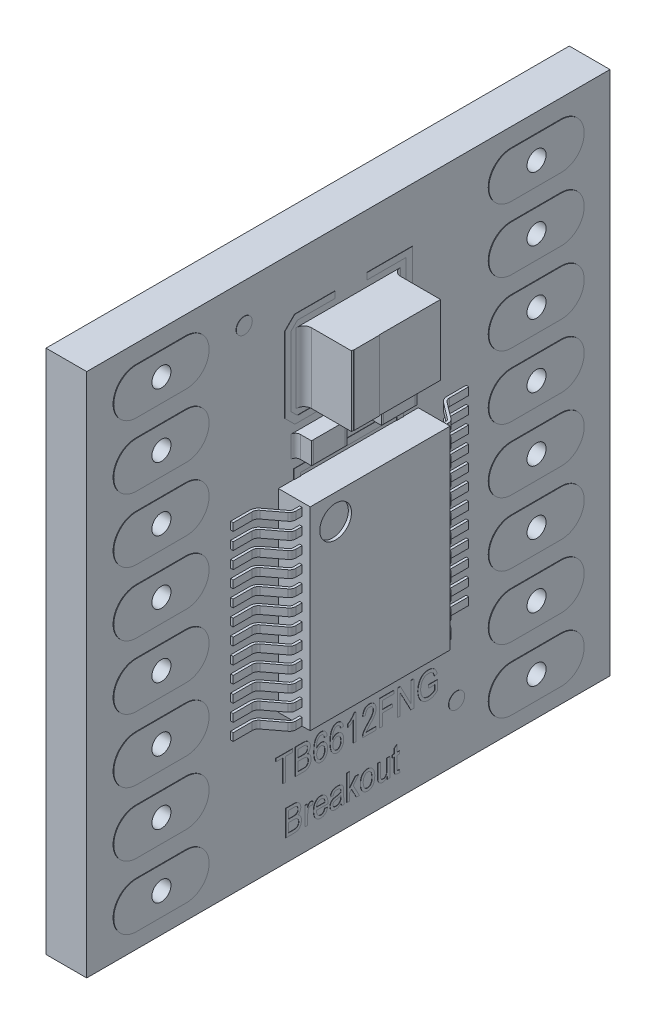
SolidWorks part; units mm, degrees
ref_plane "Front Plane" through (0, 0, 0) normal (0, 0, 1) x (1, 0, 0)
ref_plane "Top Plane" through (0, 0, 0) normal (0, 1, 0) x (1, 0, 0)
ref_plane "Right Plane" through (0, 0, 0) normal (1, 0, 0) x (0, 0, -1)
sketch "Sketch1" plane through (0, 0, 0) normal (1, 0, 0) x (0, 0, -1)
  line L1 (-10.4521, 10.4902) -> (10.4521, 10.4902)
  line L2 (-10.4521, 10.4902) -> (-10.4521, -10.4902)
  line L3 (-10.4521, -10.4902) -> (10.4521, -10.4902)
  line L4 (10.4521, 10.4902) -> (10.4521, -10.4902)
  line L5 (-10.4521, 10.4902) -> (10.4521, -10.4902) construction
  line L6 (-10.4521, -10.4902) -> (10.4521, 10.4902) construction
  point P0 (0, 0)
  dimension "D1" = 20.9804
  dimension "D2" = 20.9042
extrude "Boss-Extrude1" add sketch "Sketch1" along normal blind 1.6256
sketch "Sketch2" plane through (1.6256, 0, 0) normal (1, 0, 0) x (0, 0, -1)
  line L0 (-10.4521, -10.4902) -> (10.4521, -10.4902) construction
  line L1 (-2.794, 2.6162) -> (2.794, 2.6162)
  line L2 (-2.794, 2.6162) -> (-2.794, -5.1308)
  line L3 (-2.794, -5.1308) -> (2.794, -5.1308)
  line L4 (2.794, 2.6162) -> (2.794, -5.1308)
  line L5 (-2.794, 2.6162) -> (2.794, -5.1308) construction
  line L6 (-2.794, -5.1308) -> (2.794, 2.6162) construction
  point P0 (0, 0)
  dimension "D1" = 5.588
  dimension "D2" = 7.747
  dimension "D3" = 5.3594
extrude "Boss-Extrude2" add sketch "Sketch2" along normal blind 1.27
sketch "Sketch7" plane through (2.8956, 0, 0) normal (1, 0, 0) x (0, 0, -1)
  line L0 (-2.794, 2.6162) -> (-2.794, -5.1308) construction
  line L1 (2.794, 2.6162) -> (-2.794, 2.6162) construction
  circle A0 centre (-1.778, 1.6002) radius 0.635
  dimension "D1" = 1.27
  dimension "D2" = 1.016
  dimension "D3" = 1.016
extrude "Cut-Extrude2" cut sketch "Sketch7" against normal blind 0.127
sketch "Sketch4" plane through (1.6256, 0, 0) normal (1, 0, 0) x (0, 0, -1)
  line L0 (-7.493, 8.8392) -> (0, 8.8392) construction
  line L1 (0, 8.8392) -> (7.493, 8.8392) construction
  line L2 (0, 0) -> (0, 8.8392) construction
  line L3 (10.4521, 10.4902) -> (-10.4521, 10.4902) construction
  circle A0 centre (-7.493, 8.8392) radius 0.381
  circle A1 centre (7.493, 8.8392) radius 0.381
  dimension "D2" = 0.762
  dimension "D1" = 14.986
  dimension "D3" = 1.27
extrude "Cut-Extrude1" cut sketch "Sketch4" against normal through all
sketch "Sketch5" plane through (1.6256, 0, 0) normal (1, 0, 0) x (0, 0, -1)
  line L0 (-8.4836, 8.8392) -> (-6.5024, 8.8392) construction
  line L1 (-8.4836, 9.7536) -> (-6.5024, 9.7536)
  line L2 (-8.4836, 7.9248) -> (-6.5024, 7.9248)
  line L3 (6.5024, 8.8392) -> (8.4836, 8.8392) construction
  line L4 (6.5024, 9.7536) -> (8.4836, 9.7536)
  line L5 (6.5024, 7.9248) -> (8.4836, 7.9248)
  arc A0 (-8.4836, 9.7536) -> (-8.4836, 7.9248) centre (-8.4836, 8.8392) ccw
  arc A1 (-6.5024, 7.9248) -> (-6.5024, 9.7536) centre (-6.5024, 8.8392) ccw
  arc A2 (6.5024, 9.7536) -> (6.5024, 7.9248) centre (6.5024, 8.8392) ccw
  arc A3 (8.4836, 7.9248) -> (8.4836, 9.7536) centre (8.4836, 8.8392) ccw
  circle A6 centre (7.493, 8.8392) radius 0.381 construction
  circle A7 centre (-7.493, 8.8392) radius 0.381 construction
  circle A8 centre (7.493, 8.8392) radius 0.381
  circle A9 centre (-7.493, 8.8392) radius 0.381
  point P3 (-7.493, 8.8392)
  point P8 (7.493, 8.8392)
  point P18 (7.493, 8.8392)
  dimension "D2" = 3.81
  dimension "D1" = 1.8288
extrude "Boss-Extrude3" add sketch "Sketch5" along normal blind 0.0254
sketch "Sketch6" plane through (0, 0, 0) normal (-1, 0, 0) x (0, 0, 1)
  line L0 (-6.5024, 7.9248) -> (-8.4836, 7.9248) construction
  line L1 (-8.4836, 9.7536) -> (-6.5024, 9.7536) construction
  line L2 (8.4836, 7.9248) -> (6.5024, 7.9248) construction
  line L3 (6.5024, 9.7536) -> (8.4836, 9.7536) construction
  line L4 (-6.5024, 7.9248) -> (-8.4836, 7.9248)
  line L5 (-8.4836, 9.7536) -> (-6.5024, 9.7536)
  line L6 (8.4836, 7.9248) -> (6.5024, 7.9248)
  line L7 (6.5024, 9.7536) -> (8.4836, 9.7536)
  circle A0 centre (-7.493, 8.8392) radius 0.381 construction
  arc A1 (-6.5024, 7.9248) -> (-6.5024, 9.7536) centre (-6.5024, 8.8392) ccw construction
  arc A2 (-8.4836, 9.7536) -> (-8.4836, 7.9248) centre (-8.4836, 8.8392) ccw construction
  circle A3 centre (7.493, 8.8392) radius 0.381 construction
  arc A4 (6.5024, 9.7536) -> (6.5024, 7.9248) centre (6.5024, 8.8392) ccw construction
  arc A5 (8.4836, 7.9248) -> (8.4836, 9.7536) centre (8.4836, 8.8392) ccw construction
  circle A6 centre (-7.493, 8.8392) radius 0.381
  arc A7 (-6.5024, 7.9248) -> (-6.5024, 9.7536) centre (-6.5024, 8.8392) ccw
  arc A8 (-8.4836, 9.7536) -> (-8.4836, 7.9248) centre (-8.4836, 8.8392) ccw
  circle A9 centre (7.493, 8.8392) radius 0.381
  arc A10 (6.5024, 9.7536) -> (6.5024, 7.9248) centre (6.5024, 8.8392) ccw
  arc A11 (8.4836, 7.9248) -> (8.4836, 9.7536) centre (8.4836, 8.8392) ccw
extrude "Boss-Extrude4" add sketch "Sketch6" along normal blind 0.0254
pattern_linear "LPattern1" count 8 spacing 2.54 along (0, -1, 0) of "Cut-Extrude1", "Boss-Extrude3", "Boss-Extrude4"
sketch "Sketch11" plane through (1.6256, 0, 0) normal (1, 0, 0) x (0, 0, -1)
  circle A0 centre (-4.1683, 8.9453) radius 0.3175
  circle A1 centre (4.3185, -8.2635) radius 0.3175
  dimension "D1" = 0.635
extrude "Boss-Extrude8" add sketch "Sketch11" along normal blind 0.0127
sketch "Sketch9" plane through (1.6256, 0, 0) normal (1, 0, 0) x (0, 0, -1)
  line L0 (-1.397, 3.81) -> (0, 3.81) construction
  line L1 (-2.032, 4.2418) -> (-0.762, 4.2418)
  line L2 (-2.032, 4.2418) -> (-2.032, 3.3782)
  line L3 (-2.032, 3.3782) -> (-0.762, 3.3782)
  line L4 (-0.762, 4.2418) -> (-0.762, 3.3782)
  line L5 (-2.032, 4.2418) -> (-0.762, 3.3782) construction
  line L6 (-2.032, 3.3782) -> (-0.762, 4.2418) construction
  line L7 (0.762, 4.2418) -> (2.032, 4.2418)
  line L8 (0.762, 4.2418) -> (0.762, 3.3782)
  line L9 (0.762, 3.3782) -> (2.032, 3.3782)
  line L10 (2.032, 4.2418) -> (2.032, 3.3782)
  line L11 (0.762, 4.2418) -> (2.032, 3.3782) construction
  line L12 (0.762, 3.3782) -> (2.032, 4.2418) construction
  line L13 (0, 3.81) -> (1.397, 3.81) construction
  line L14 (0, 3.81) -> (0, 0) construction
  line L15 (2.794, 2.6162) -> (-2.794, 2.6162) construction
  point P0 (-1.397, 3.81)
  point P5 (1.397, 3.81)
  dimension "D1" = 0.8636
  dimension "D2" = 1.27
  dimension "D3" = 1.397
  dimension "D4" = 0.762
extrude "Boss-Extrude6" add sketch "Sketch9" along normal blind 0.635
sketch "Sketch10" plane through (1.6256, 0, 0) normal (1, 0, 0) x (0, 0, -1)
  line L1 (-0.762, 4.2418) -> (-0.6858, 4.2418)
  line L2 (-0.762, 4.2418) -> (-0.762, 3.3782)
  line L3 (-0.762, 3.3782) -> (-0.6858, 3.3782)
  line L4 (-0.6858, 4.2418) -> (-0.6858, 3.3782)
  line L5 (-2.032, 4.2418) -> (-2.1082, 4.2418)
  line L6 (-2.032, 4.2418) -> (-2.032, 3.3782)
  line L7 (-2.032, 3.3782) -> (-2.1082, 3.3782)
  line L8 (-2.1082, 4.2418) -> (-2.1082, 3.3782)
  line L9 (0.762, 4.2418) -> (0.6858, 4.2418)
  line L10 (0.762, 4.2418) -> (0.762, 3.3782)
  line L11 (0.762, 3.3782) -> (0.6858, 3.3782)
  line L12 (0.6858, 4.2418) -> (0.6858, 3.3782)
  line L13 (2.032, 4.2418) -> (2.1082, 4.2418)
  line L14 (2.032, 4.2418) -> (2.032, 3.3782)
  line L15 (2.032, 3.3782) -> (2.1082, 3.3782)
  line L16 (2.1082, 4.2418) -> (2.1082, 3.3782)
  line L17 (-2.032, 3.3782) -> (-0.762, 3.3782) construction
  dimension "D1" = 0.0762
extrude "Boss-Extrude7" add sketch "Sketch10" along normal blind 0.6363
fillet "Fillet1" radius 0.1905 4 edges at (1.6256, 3.81, -2.1082) (1.6256, 3.81, -0.6858) (1.6256, 3.81, 0.6858) (1.6256, 3.81, 2.1082)
sketch "Sketch12" plane through (1.6256, 0, 0) normal (1, 0, 0) x (0, 0, -1)
  line L0 (0, 0) -> (0, 6.4262) construction
  line L1 (-1.778, 5.0292) -> (1.778, 5.0292)
  line L2 (-1.778, 5.0292) -> (-1.778, 7.8232)
  line L3 (-1.778, 7.8232) -> (1.778, 7.8232)
  line L4 (1.778, 5.0292) -> (1.778, 7.8232)
  line L5 (-1.778, 5.0292) -> (1.778, 7.8232) construction
  line L6 (-1.778, 7.8232) -> (1.778, 5.0292) construction
  line L8 (10.4521, 10.4902) -> (-10.4521, 10.4902) construction
  point P0 (0, 6.4262)
  dimension "D1" = 2.794
  dimension "D2" = 3.556
  dimension "D3" = 2.667
extrude "Boss-Extrude9" add sketch "Sketch12" along normal blind 1.905
fillet "Fillet2" radius 0.3048 2 edges at (1.6256, 6.4262, -1.778) (1.6256, 6.4262, 1.778)
sketch "Sketch13" plane through (3.5306, 0, 0) normal (1, 0, 0) x (0, 0, -1)
  line L0 (1.778, 7.8232) -> (-1.778, 7.8232) construction
  line L1 (-1.6958, 7.8232) -> (-0.6798, 7.8232)
  line L2 (-1.6958, 7.8232) -> (-1.6958, 5.0292)
  line L3 (-1.6958, 5.0292) -> (-0.6798, 5.0292)
  line L4 (-0.6798, 7.8232) -> (-0.6798, 5.0292)
  line L5 (-2.0828, 5.0292) -> (2.0828, 5.0292) construction
  dimension "D1" = 1.016
extrude "Boss-Extrude10" add sketch "Sketch13" along normal blind 0.0127
sketch "Sketch14" plane through (0, -5.1308, 0) normal (0, -1, 0) x (1, 0, 0)
  line L0 (2.5745, -2.794) -> (2.5745, -3.048)
  line L1 (2.8956, -2.794) -> (1.6256, -2.794) construction
  line L2 (2.4739, -3.2504) -> (1.8278, -3.74)
  line L3 (1.7272, -3.9425) -> (1.7272, -4.7045)
  line L4 (2.4729, -2.794) -> (2.4729, -3.048)
  line L5 (2.4126, -3.1695) -> (1.7664, -3.659)
  line L6 (1.6256, -3.9425) -> (1.6256, -4.7045)
  line L7 (2.5745, -2.794) -> (2.4729, -2.794)
  line L8 (1.7272, -4.7045) -> (1.6256, -4.7045)
  line L9 (1.6256, 10.4521) -> (1.6256, -10.4521) construction
  line L10 (2.8956, 0) -> (-1.1531, 0) construction
  line L11 (2.8956, 2.794) -> (2.8956, -2.794) construction
  line L12 (2.5745, 2.794) -> (2.4729, 2.794)
  line L13 (2.5745, 2.794) -> (2.5745, 3.048)
  line L14 (2.4729, 2.794) -> (2.4729, 3.048)
  line L15 (2.4739, 3.2504) -> (1.8278, 3.74)
  line L16 (2.4126, 3.1695) -> (1.7664, 3.659)
  line L17 (1.7272, 3.9425) -> (1.7272, 4.7045)
  line L18 (1.7272, 4.7045) -> (1.6256, 4.7045)
  line L19 (1.6256, 3.9425) -> (1.6256, 4.7045)
  arc A0 (1.8278, -3.74) -> (1.7272, -3.9425) centre (1.9812, -3.9425) ccw
  arc A1 (2.5745, -3.048) -> (2.4739, -3.2504) centre (2.3205, -3.048) cw
  arc A2 (2.4729, -3.048) -> (2.4126, -3.1695) centre (2.3205, -3.048) cw
  arc A3 (1.7664, -3.659) -> (1.6256, -3.9425) centre (1.9812, -3.9425) ccw
  arc A4 (2.4729, 3.048) -> (2.4126, 3.1695) centre (2.3205, 3.048) ccw
  arc A5 (2.5745, 3.048) -> (2.4739, 3.2504) centre (2.3205, 3.048) ccw
  arc A6 (1.7664, 3.659) -> (1.6256, 3.9425) centre (1.9812, 3.9425) cw
  arc A7 (1.8278, 3.74) -> (1.7272, 3.9425) centre (1.9812, 3.9425) cw
  dimension "D1" = 0.254
  dimension "D3" = 232.848
  dimension "D4" = 0.254
  dimension "D5" = 0.762
  dimension "D2" = 0.1016
extrude "Boss-Extrude11" add sketch "Sketch14" against normal blind 0.3048
pattern_linear "LPattern2" count 12 spacing 0.6604 along (0, 1, 0) of "Boss-Extrude11"
sketch "Sketch8" plane through (1.6256, 0, 0) normal (1, 0, 0) x (0, 0, -1)
  line L0 (-2.1843, 2.9972) -> (2.1843, 2.9972)
  line L1 (-1.9303, 2.7432) -> (1.9303, 2.7432)
  line L2 (-1.9303, 2.7432) -> (-1.9303, -5.2578)
  line L3 (-1.9303, -5.2578) -> (1.9303, -5.2578)
  line L4 (1.9303, 2.7432) -> (1.9303, -5.2578)
  line L5 (-1.9303, 2.7432) -> (1.9303, -5.2578) construction
  line L6 (-1.9303, -5.2578) -> (1.9303, 2.7432) construction
  line L7 (2.1843, 2.9972) -> (2.1843, -5.5118)
  line L8 (-2.1843, -5.5118) -> (2.1843, -5.5118)
  line L9 (-2.1843, 2.9972) -> (-2.1843, -5.5118)
  line L10 (2.794, 2.6162) -> (-2.794, 2.6162) construction
  line L11 (-0.5427, 8.3278) -> (-0.5427, 8.0738)
  line L12 (-2.794, -5.1308) -> (2.794, -5.1308) construction
  line L13 (2.5533, 8.3278) -> (2.5533, 4.5246)
  line L14 (-2.0453, 8.0738) -> (-0.5427, 8.0738)
  line L15 (-2.2993, 7.8198) -> (-2.2993, 5.0326)
  line L16 (-2.0453, 4.7786) -> (-0.5427, 4.7786)
  line L17 (2.2993, 8.0738) -> (2.2993, 4.7786)
  line L18 (-2.2993, 8.0738) -> (-2.2993, 4.7786) construction
  line L19 (-2.2993, 7.8198) -> (-2.0453, 8.0738)
  line L20 (-2.1505, 4.5246) -> (-0.5427, 4.5246)
  line L21 (-2.5533, 7.925) -> (-2.1505, 8.3278)
  line L22 (-2.1505, 8.3278) -> (-0.5427, 8.3278)
  line L23 (0.7387, 8.3278) -> (0.7387, 8.0738)
  line L24 (0.7387, 8.3278) -> (2.5533, 8.3278)
  line L25 (-2.5533, 8.3278) -> (2.5533, 8.3278) construction
  line L26 (0.7387, 8.0738) -> (2.2993, 8.0738)
  line L27 (-2.2993, 8.0738) -> (2.2993, 8.0738) construction
  line L28 (-2.2993, 5.0326) -> (-2.0453, 4.7786)
  line L29 (-2.5533, 4.9274) -> (-2.1505, 4.5246)
  line L30 (0.7387, 4.7786) -> (2.2993, 4.7786)
  line L31 (-2.2993, 4.7786) -> (2.2993, 4.7786) construction
  line L32 (0.7387, 4.5246) -> (2.5533, 4.5246)
  line L33 (-2.5533, 4.5246) -> (2.5533, 4.5246) construction
  line L34 (0.7387, 4.7786) -> (0.7387, 4.5246)
  line L35 (-0.5427, 4.7786) -> (-0.5427, 4.5246)
  line L36 (-2.5533, 8.3278) -> (-2.5533, 4.5246) construction
  line L37 (-2.5533, 7.925) -> (-2.5533, 4.9274)
  line L38 (-2.4789, 7.9994) -> (-2.2249, 8.2534) construction
  line L39 (-2.4789, 4.853) -> (-2.2249, 4.599) construction
  line L40 (-2.5533, 7.8198) -> (-2.5533, 5.0326) construction
  text T0 "TB6612FNG\r\n Breakout" font "Arial Narrow" height 1.016
  point P1 (0, -1.2573)
  point P14 (0, 6.4262)
  dimension "D2" = 0.127
  dimension "D3" = 0.127
  dimension "D5" = 0.254
  dimension "D1" = 0.254
  dimension "D4" = 0.254
  dimension "D6" = 0.254
  dimension "D7" = 0.254
extrude "Boss-Extrude5" add sketch "Sketch8" along normal blind 0.0127
